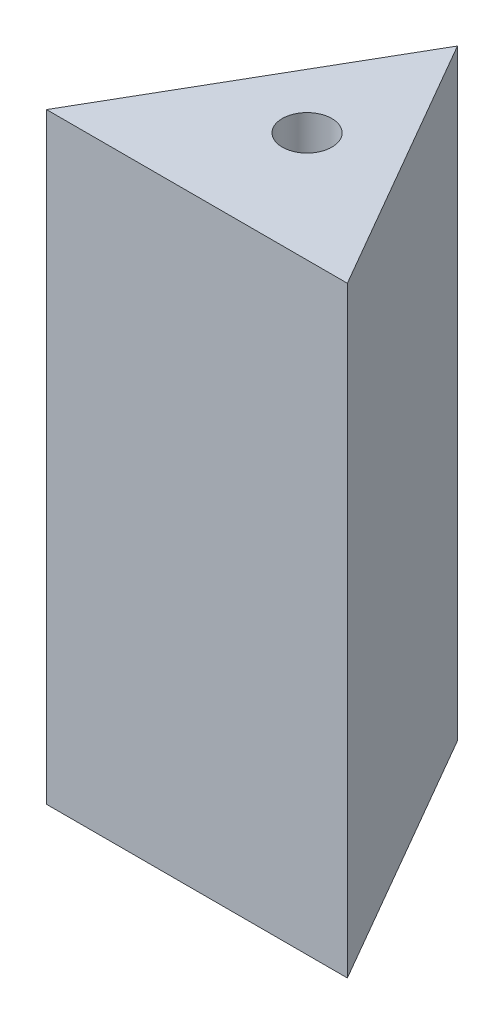
SolidWorks part; units mm, degrees
ref_plane "前视基准面" through (0, 0, 0) normal (0, 0, 1) x (1, 0, 0)
ref_plane "上视基准面" through (0, 0, 0) normal (0, 1, 0) x (1, 0, 0)
ref_plane "右视基准面" through (0, 0, 0) normal (1, 0, 0) x (0, 0, -1)
sketch "草图1" plane through (0, 0, 0) normal (0, 1, 0) x (1, 0, 0)
  line L0 (0, 0) -> (20, 0)
  line L1 (10, 17.3205) -> (20, 0)
  line L2 (0, 0) -> (10, 17.3205)
  line L3 (10, 17.3205) -> (10, 7.3205)
extrude "凸台-拉伸1" add sketch "草图1" along normal blind 40
sketch "草图5" plane through (0, 0, 0) normal (0, -1, 0) x (1, 0, 0)
  line L0 (10, -17.3205) -> (10, -7.3205)
hole_wizard "M4 螺纹孔1" positions "草图6" profile "草图7" tap size "M4" standard "GB"
sketch "草图6" plane through (0, 0, 0) normal (0, -1, 0) x (-1, 0, 0)
  point P0 (-10, 7.3205)
sketch "草图7" plane through (10, 0, -7.3205) normal (1, 0, 0) x (0, 0, -1)
  line L0 (0, 0) -> (0, 11.0914)
  line L1 (0, 11.0914) -> (1.65, 10.1)
  line L2 (1.65, 10.1) -> (1.65, 0)
  line L5 (1.65, 0) -> (0, 0)
  line L10 (0, 11.0914) -> (-1.65, 10.1) construction
  line L11 (0, -6.35) -> (0, 107.95) construction
  dimension "螺纹孔钻头直径" = 3.3
  dimension "螺纹孔钻头深度" = 10.1
  dimension "导头角度" = 118
cosmetic thread "孔螺蚊线1" parameters "D1"=8, "D2"=4
hole_wizard "M4 螺纹孔2" positions "草图8" profile "草图9" tap size "M4" standard "GB"
sketch "草图8" plane through (0, 40, 0) normal (0, 1, 0) x (1, 0, 0)
  point P0 (10, 7.3205)
sketch "草图9" plane through (10, 40, -7.3205) normal (1, 0, 0) x (0, 0, 1)
  line L0 (0, 0) -> (0, 11.0914)
  line L1 (0, 11.0914) -> (1.65, 10.1)
  line L2 (1.65, 10.1) -> (1.65, 0)
  line L5 (1.65, 0) -> (0, 0)
  line L10 (0, 11.0914) -> (-1.65, 10.1) construction
  line L11 (0, -6.35) -> (0, 107.95) construction
  dimension "螺纹孔钻头直径" = 3.3
  dimension "螺纹孔钻头深度" = 10.1
  dimension "导头角度" = 118
cosmetic thread "孔螺蚊线2" parameters "D1"=8, "D2"=4
